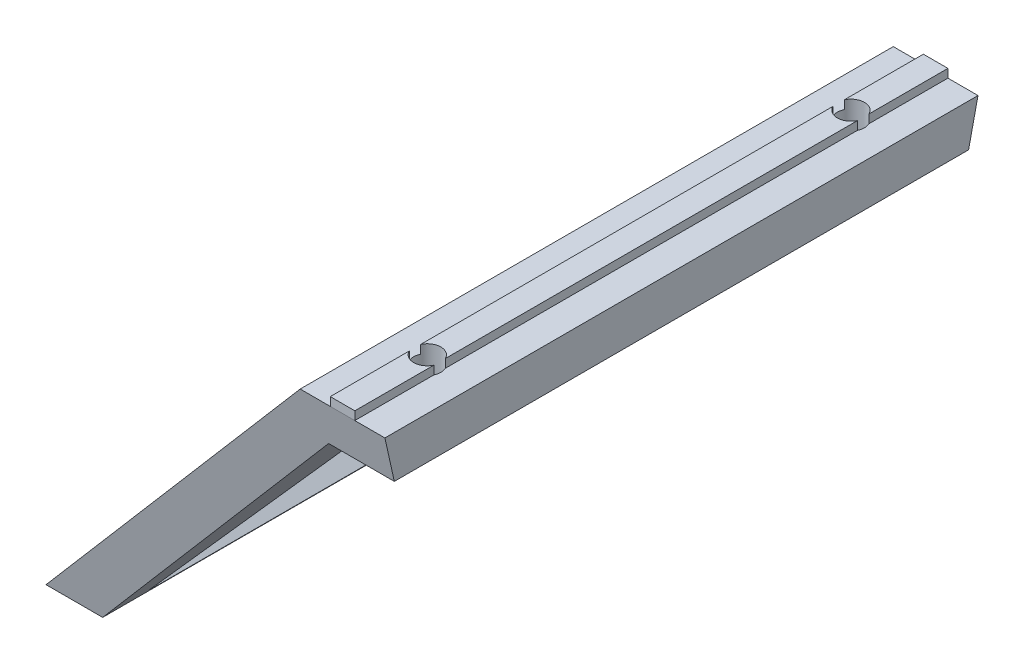
SolidWorks part; units mm, degrees
ref_plane "Front Plane" through (0, 0, 0) normal (0, 0, 1) x (1, 0, 0)
ref_plane "Top Plane" through (0, 0, 0) normal (0, 1, 0) x (1, 0, 0)
ref_plane "Right Plane" through (0, 0, 0) normal (1, 0, 0) x (0, 0, -1)
sketch "Sketch1" plane through (0, 0, 0) normal (0, 0, 1) x (1, 0, 0)
  line L0 (50, 45) -> (50, 40)
  line L1 (50, 40) -> (42.2453, 40)
  line L2 (42.2453, 40) -> (6.6898, 0)
  line L3 (6.6898, 0) -> (0, 0)
  line L4 (0, 0) -> (40, 45)
  line L5 (40, 45) -> (43.55, 45)
  line L6 (43.55, 45) -> (43.55, 46)
  line L7 (43.55, 46) -> (46.45, 46)
  line L8 (46.45, 46) -> (46.45, 45)
  line L9 (46.45, 45) -> (50, 45)
  line L10 (6.6898, 0) -> (34.2968, 0) construction
  dimension "D1" = 10
  dimension "D2" = 2.9
  dimension "D3" = 5
  dimension "D4" = 40
  dimension "D5" = 5
  dimension "D6" = 45
  dimension "D7" = 1
extrude "Main" add sketch "Sketch1" along normal mid plane 70
sketch "Sketch2" plane through (0, 12.0711, 0) normal (1, 0, 0) x (0, 0, 1)
  line L0 (-35, -32.9289) -> (-25, 12.0711)
  line L1 (35, -32.9289) -> (-35, -32.9289) construction
  line L2 (-35, -32.9289) -> (-35, 12.0711) construction
  line L3 (35, 12.0711) -> (-35, 12.0711) construction
  line L5 (-35, 12.0711) -> (-35, -32.9289)
  line L6 (35, -32.9289) -> (35, 12.0711)
  line L8 (25, 12.0711) -> (35, -32.9289)
  line L15 (-25, 12.0711) -> (-35, 12.0711)
  line L16 (25, 12.0711) -> (35, 12.0711)
  dimension "D2" = 50
  dimension "D5" = 10
extrude "SideCut" cut sketch "Sketch2" against normal through all and the other way through all
sketch "Sketch5" plane through (0, 0, 0) normal (-0.7474, 0.6644, 0) x (0, 0, 1)
  line L0 (25, 0) -> (-25, 0) construction
  line L1 (-20, 55.208) -> (20, 55.208)
  line L2 (-20, 55.208) -> (-20, 5)
  line L3 (-20, 5) -> (20, 5)
  line L4 (20, 55.208) -> (20, 5)
  line L5 (35, 60.208) -> (-35, 60.208) construction
  line L6 (0, -55) -> (0, 55) construction
  point P8 (0, 55.208)
  dimension "D1" = 5
  dimension "D2" = 5
  dimension "D3" = 40
extrude "CentralCut" cut sketch "Sketch5" against normal through all
sketch "Sketch3" plane through (0, 46, 0) normal (0, 1, 0) x (1, 0, 0)
  line L0 (46.45, -35) -> (43.55, -35) construction
  line L1 (46.45, 35) -> (43.55, 35) construction
  line L2 (50, -35) -> (50, 35) construction
  circle A0 centre (45, 25) radius 1.6
  circle A1 centre (45, -25) radius 1.6
  point P6 (45, -35)
  point P9 (45, 35)
  dimension "D1" = 3.2
  dimension "D2" = 10
  dimension "D3" = 10
  dimension "D4" = 5
extrude "MakerBeamFixHoles" cut sketch "Sketch3" against normal through all both and the other way through all
sketch "Sketch4" plane through (0, 0, 0) normal (0, 0, 1) x (1, 0, 0)
  line L0 (34.6851, 39.0207) -> (32.692, 36.7785)
  line L1 (32.692, 36.7785) -> (33.8131, 35.782)
  line L3 (42.2453, 40) -> (6.6898, 0) construction
  line L4 (34.6851, 39.0207) -> (35.8062, 38.0242)
  line L5 (40, 45) -> (0, 0) construction
  arc A0 (33.8131, 35.782) -> (35.8062, 38.0242) centre (34.8097, 36.9031) ccw
  dimension "D1" = 1.5
  dimension "D2" = 1.5
  dimension "D3" = 3
extrude "RollerSupportHoles" cut sketch "Sketch4" against normal mid plane 45
pattern_linear "LPattern1" count 5 spacing 10 along (-0.6644, -0.7474, 0) of "RollerSupportHoles"
